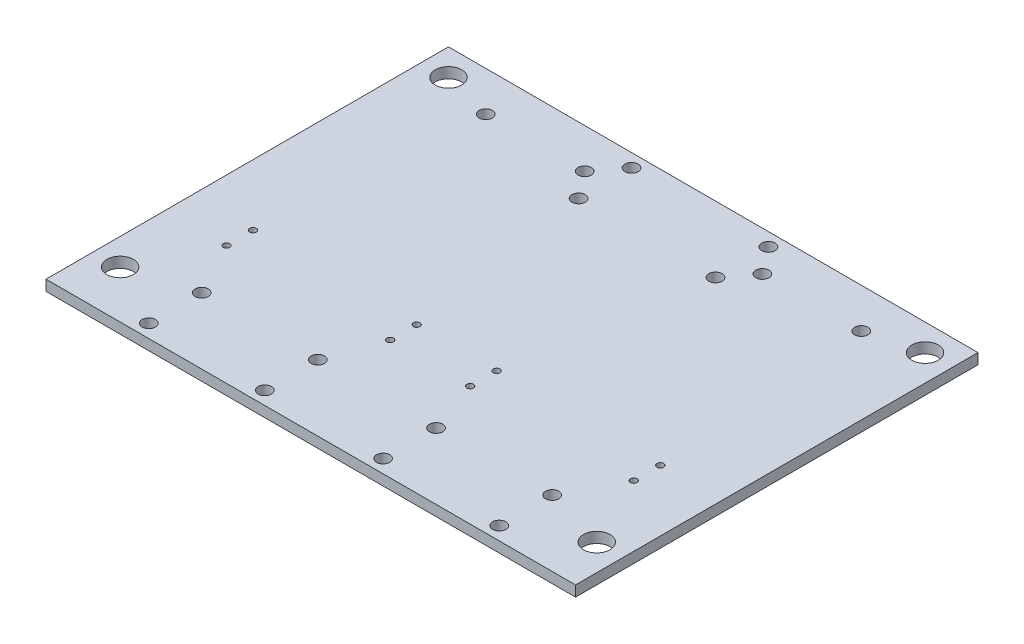
SolidWorks part; units mm, degrees
other "Markup1"
sketch "Sketch18" plane through (-127, 2.54, 10.16) normal (0, 1, 0) x (1, 0, 0)
ref_plane "Front Plane" through (0, 0, 0) normal (0, 0, 1) x (1, 0, 0)
ref_plane "Top Plane" through (0, 0, 0) normal (0, 1, 0) x (1, 0, 0)
ref_plane "Right Plane" through (0, 0, 0) normal (1, 0, 0) x (0, 0, -1)
sketch "Sketch1" plane through (0, 0, 0) normal (0, 0, 1) x (1, 0, 0)
  line L6 (127, 2.54) -> (-127, 2.54)
  line L24 (127, 2.54) -> (127, -2.54)
  line L25 (127, -2.54) -> (-127, -2.54)
  line L26 (-127, 2.54) -> (-127, -2.54)
  line L27 (127, 2.54) -> (-127, -2.54) construction
  line L28 (127, -2.54) -> (-127, 2.54) construction
  point P0 (0, 0)
  point P1 (0, 0)
  dimension "D1" = 5.08
  dimension "D2" = 254
extrude "Boss-Extrude1" add sketch "Sketch1" along normal blind 203.2
sketch "Sketch2" plane through (0, 2.54, 0) normal (0, 1, 0) x (1, 0, 0)
  line L0 (127, -203.2) -> (-127, -203.2) construction
  line L1 (-127, 0) -> (-101.6, 0)
  line L2 (-127, 0) -> (-127, -203.2)
  line L3 (-127, -203.2) -> (-101.6, -203.2)
  line L4 (-101.6, 0) -> (-101.6, -203.2)
  line L6 (127, 0) -> (101.6, 0)
  line L7 (127, 0) -> (127, -203.2)
  line L8 (127, -203.2) -> (101.6, -203.2)
  line L9 (101.6, 0) -> (101.6, -203.2)
  dimension "D1" = 25.4
sketch "Sketch3" plane through (0, 2.54, 0) normal (0, 1, 0) x (1, 0, 0)
  line L1 (-127, -22.86) -> (-101.6, -22.86) construction
  line L2 (-127, 0) -> (-127, -203.2) construction
  line L3 (-101.6, 0) -> (-101.6, -203.2) construction
  line L4 (-114.3, -22.86) -> (-114.3, -180.34) construction
  line L5 (0, 0) -> (0, -203.2) construction
  line L6 (127, 0) -> (-127, 0) construction
  line L7 (127, -203.2) -> (-127, -203.2) construction
  line L8 (-127, 0) -> (-101.6, 0) construction
  line L9 (101.6, -21.6084) -> (127, -21.6084) construction
  line L10 (101.6, 0) -> (101.6, -203.2) construction
  line L11 (127, 0) -> (127, -203.2) construction
  circle A0 centre (-114.3, -22.86) radius 6.35
  circle A1 centre (-114.3, -180.34) radius 6.35
  circle A2 centre (114.3, -22.86) radius 6.35
  circle A3 centre (114.3, -180.34) radius 6.35
  point P14 (-114.3, -22.86)
  point P21 (-114.3, -101.6)
  point P22 (0, -101.6)
  point P26 (114.3, -21.6084)
  dimension "D1" = 12.7
  dimension "D2" = 22.86
extrude "Cut-Extrude1" cut sketch "Sketch3" against normal through all
sketch "Sketch5" plane through (0, 2.54, 0) normal (0, 1, 0) x (1, 0, 0)
  circle A2 centre (97.63, -133.2) radius 1.5875
  circle A3 centre (97.63, -133.2) radius 1.5875
  circle A4 centre (97.63, -145.9) radius 1.5875
  circle A5 centre (97.63, -145.9) radius 1.5875
  circle A6 centre (-19.21, -133.2) radius 1.5875
  circle A7 centre (-19.21, -133.2) radius 1.5875
  circle A8 centre (-19.21, -145.9) radius 1.5875
  circle A9 centre (-19.21, -145.9) radius 1.5875
  circle A13 centre (-97.696, -133.2) radius 1.5875
  circle A14 centre (-97.696, -145.9) radius 1.5875
  circle A15 centre (19.144, -133.2) radius 1.5875
  circle A16 centre (19.144, -145.9) radius 1.5875
  dimension "D5" = 78.486
  dimension "D6" = 78.486
  dimension "D1" = 0
  dimension "D2" = 0
  dimension "D3" = 0
  dimension "D4" = 0
extrude "Cut-Extrude2" cut sketch "Sketch5" against normal blind 152.4
sketch "Sketch7" plane through (0, -2.54, 0) normal (0, -1, 0) x (1, 0, 0)
  line L1 (-127, 203.2) -> (-101.6, 203.2)
  line L2 (-127, 203.2) -> (-127, 0)
  line L3 (-127, 0) -> (-101.6, 0)
  line L4 (-101.6, 203.2) -> (-101.6, 0)
  line L5 (127, 203.2) -> (101.6, 203.2)
  line L6 (127, 203.2) -> (127, 0)
  line L7 (127, 0) -> (101.6, 0)
  line L8 (101.6, 203.2) -> (101.6, 0)
  circle A0 centre (-114.3, 180.34) radius 6.35
  circle A1 centre (-114.3, 22.86) radius 6.35
  circle A2 centre (114.3, 22.86) radius 6.35
  circle A3 centre (114.3, 180.34) radius 6.35
  dimension "D1" = 12.7
extrude "Boss-Extrude2" [suppressed] add sketch "Sketch7" along normal blind 7.62
sketch "Sketch8" plane through (0, 2.54, 0) normal (0, 1, 0) x (1, 0, 0)
  circle A0 centre (-89.6874, -180.34) radius 3.175
  circle A1 centre (-89.6874, -154.94) radius 3.175
  point P3 (-114.3, -180.34)
  dimension "D1" = 6.35
  dimension "D2" = 24.6126
  dimension "D3" = 25.4
sketch "Sketch9" plane through (0, 2.54, 0) normal (0, 1, 0) x (1, 0, 0)
  line L0 (127, 0) -> (-127, 0) construction
  line L1 (-91.63, 0) -> (-83.63, 0)
  line L2 (-91.63, 0) -> (-91.63, -12.7)
  line L3 (-91.63, -12.7) -> (-83.63, -12.7)
  line L4 (-83.63, 0) -> (-83.63, -12.7)
  line L5 (-87.63, 0) -> (-87.63, -55.7623) construction
  line L6 (-127, -203.2) -> (-127, 0) construction
  line L7 (-61.405, -25.4) -> (-61.405, -12.7) construction
  circle A0 centre (-61.405, -12.7) radius 3.175
  circle A1 centre (-61.405, -25.4) radius 3.175
  dimension "D1" = 6.35
  dimension "D2" = 6.35
  dimension "D3" = 39.37
  dimension "D4" = 12.7
  dimension "D5" = 12.7
  dimension "D6" = 8
  dimension "D7" = 22.225
  dimension "D8" = 4
  dimension "D9" = 12.7
sketch "Sketch12" plane through (0, 2.54, 0) normal (0, 1, 0) x (1, 0, 0)
  line L0 (-90.0557, -29.21) -> (-42.6212, -29.21) construction
  line L1 (-127, -203.2) -> (-127, 0) construction
  line L4 (127, 0) -> (-127, 0) construction
  circle A0 centre (-90.0557, -29.21) radius 3.175
  circle A1 centre (-42.6212, -29.21) radius 3.175
  dimension "D1" = 6.35
  dimension "D2" = 47.4345
  dimension "D3" = 29.21
  dimension "D4" = 84.3788
extrude "Cut-Extrude7" cut sketch "Sketch12" against normal through all
sketch "Sketch14" plane through (0, 2.54, 0) normal (0, 1, 0) x (1, 0, 0)
  line L0 (127, 0) -> (-127, 0) construction
  line L1 (-127, -203.2) -> (-127, 0) construction
  circle A0 centre (-32.8328, -16.51) radius 3.175
  circle A1 centre (-32.8328, -41.91) radius 3.175
  dimension "D1" = 6.35
  dimension "D4" = 94.1672
  dimension "D2" = 25.4
  dimension "D3" = 16.51
extrude "Cut-Extrude8" cut sketch "Sketch14" against normal up to next (5.08 mm away)
mirror "Mirror1" about plane through (0, 0, 0) normal (1, 0, 0) of "Cut-Extrude8", "Cut-Extrude7"
sketch "Sketch15" plane through (0, 2.54, 0) normal (0, 1, 0) x (1, 0, 0)
  line L0 (127, -203.2) -> (127, 0) construction
  line L1 (-127, 0) -> (127, 0)
  line L2 (-127, 0) -> (-127, -10.16)
  line L3 (-127, -10.16) -> (127, -10.16)
  line L4 (127, 0) -> (127, -10.16)
  dimension "D1" = 10.16
extrude "Cut-Extrude9" cut sketch "Sketch15" against normal up to next
sketch "Sketch16" plane through (0, 2.54, 0) normal (0, 1, 0) x (1, 0, 0)
  line L0 (127, -203.2) -> (127, -10.16) construction
  line L1 (127, -203.2) -> (-127, -203.2) construction
  circle A0 centre (84.0486, -196.85) radius 3.175
  circle A1 centre (84.0486, -171.45) radius 3.175
  dimension "D2" = 6.35
  dimension "D1" = 42.9514
  dimension "D3" = 25.4
  dimension "D4" = 6.35
extrude "Cut-Extrude10" cut sketch "Sketch16" against normal through all
mirror "Mirror2" about plane through (0, 0, 0) normal (1, 0, 0) of "Cut-Extrude10"
sketch "Sketch17" plane through (0, 2.54, 0) normal (0, 1, 0) x (1, 0, 0)
  line L0 (-97.696, -133.2) -> (-19.21, -133.2) construction
  line L1 (-58.453, -133.2) -> (-58.453, -151.0054) construction
  point P6 (-19.21, -133.2)
ref_plane "Plane1" through (-58.453, 0, 0) normal (-1, 0, 0) x (0, 0, 1)
sketch "Sketch19" plane through (0, 2.54, 0) normal (0, 1, 0) x (1, 0, 0)
  line L0 (-84.0486, -171.45) -> (-28.3574, -171.45) construction
  line L1 (-84.0486, -196.85) -> (-28.3574, -196.85) construction
  line L2 (-84.0486, -182.2625) -> (-58.453, -182.2625) construction
  line L3 (-58.453, 106.172) -> (-58.453, -106.172) construction
  line L4 (-58.453, -182.2625) -> (-32.8574, -182.2625) construction
  circle A0 centre (-28.3574, -171.45) radius 3.175
  circle A1 centre (-28.3574, -196.85) radius 3.175
  circle A2 centre (-84.0486, -171.45) radius 3.175 construction
  point P9 (-21.6506, -171.45)
  dimension "D1" = 4.5
extrude "Cut-Extrude11" cut sketch "Sketch19" against normal up to next (5.08 mm away)
mirror "Mirror3" about plane through (0, 0, 0) normal (1, 0, 0) of "Cut-Extrude11"
